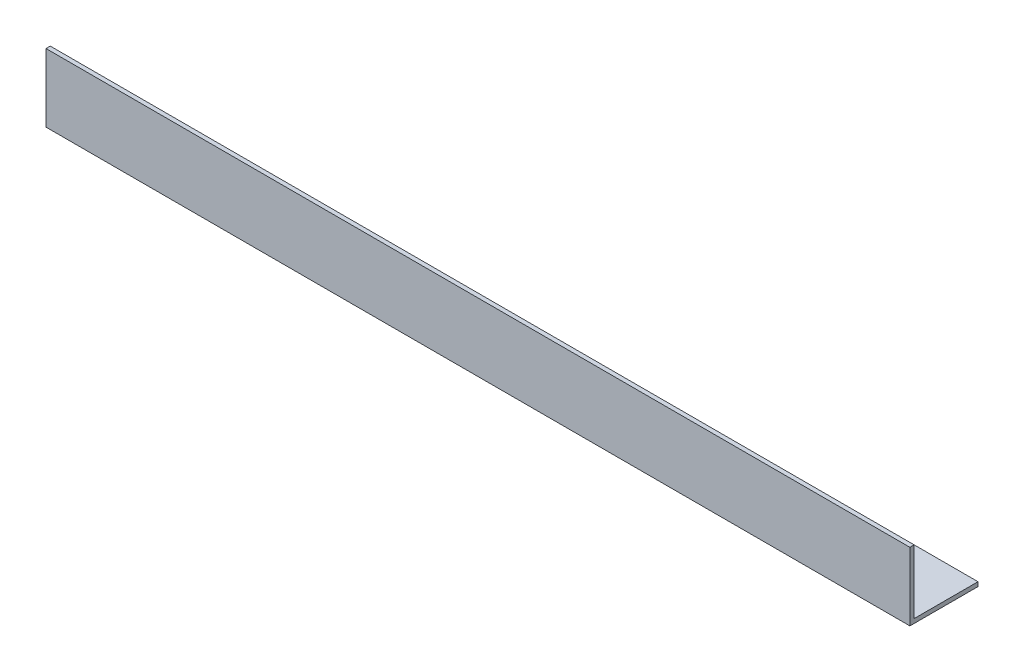
SolidWorks part; units mm, degrees
ref_plane "Alzado" through (0, 0, 0) normal (0, 0, 1) x (1, 0, 0)
ref_plane "Planta" through (0, 0, 0) normal (0, 1, 0) x (1, 0, 0)
ref_plane "Vista lateral" through (0, 0, 0) normal (1, 0, 0) x (0, 0, -1)
sketch "Croquis1" plane through (0, 0, 0) normal (1, 0, 0) x (0, 0, -1)
  line L0 (0, 16) -> (0, 0)
  line L1 (0, 0) -> (16, 0)
  line L2 (16, 0) -> (16, 1)
  line L3 (16, 1) -> (1, 1)
  line L4 (1, 1) -> (1, 16)
  line L5 (1, 16) -> (0, 16)
  dimension "D1" = 16
  dimension "D2" = 16
  dimension "D3" = 1
extrude "Saliente-Extruir1" add sketch "Croquis1" along normal blind 203
